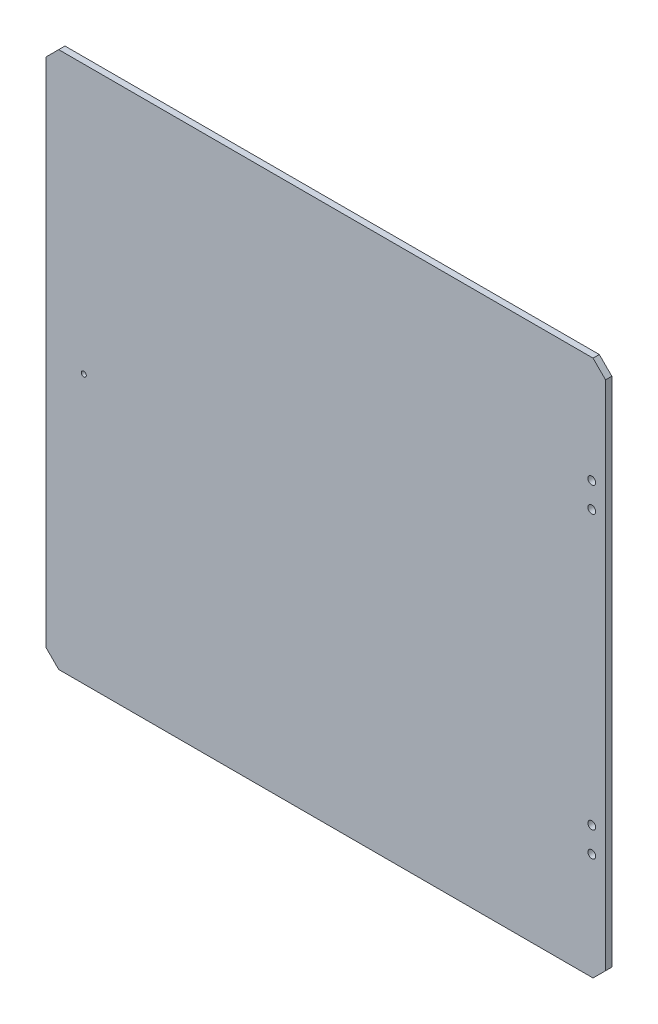
SolidWorks part; units mm, degrees
material "ABS PC"
ref_plane "Piano frontale" through (0, 0, 0) normal (0, 0, 1) x (1, 0, 0)
ref_plane "Piano superiore" through (0, 0, 0) normal (0, 1, 0) x (1, 0, 0)
ref_plane "Piano destro" through (0, 0, 0) normal (1, 0, 0) x (0, 0, -1)
sketch "Schizzo1" plane through (0, 0, 0) normal (0, 0, 1) x (1, 0, 0)
  line L0 (-223, 204) -> (-213, 214)
  line L1 (213, -214) -> (-213, -214)
  line L2 (223, 204) -> (223, -204)
  line L3 (213, 214) -> (-213, 214)
  line L4 (-223, -204) -> (-223, 204)
  line L5 (223, -214) -> (-223, 214) construction
  line L6 (223, 214) -> (-223, -214) construction
  line L7 (223, 204) -> (213, 214)
  line L8 (213, -214) -> (223, -204)
  line L9 (-213, -214) -> (-223, -204)
  line L11 (-223, 0) -> (221, 0) construction
  circle A0 centre (212, 129) radius 3.1
  circle A1 centre (212, 109) radius 3.1
  circle A2 centre (212, -109) radius 3.1
  circle A3 centre (212, -129) radius 3.1
  circle A4 centre (-193, 0) radius 2
  point P0 (0, 0)
  point P25 (223, -214)
  dimension "D9" = 4
  dimension "D12" = 6.2
  dimension "D1" = 446
  dimension "D2" = 428
  dimension "D3" = 20
  dimension "D4" = 11
  dimension "D10" = 30
  dimension "D11" = 85
extrude "Estrusione-Estrusione1" add sketch "Schizzo1" along normal blind 5
